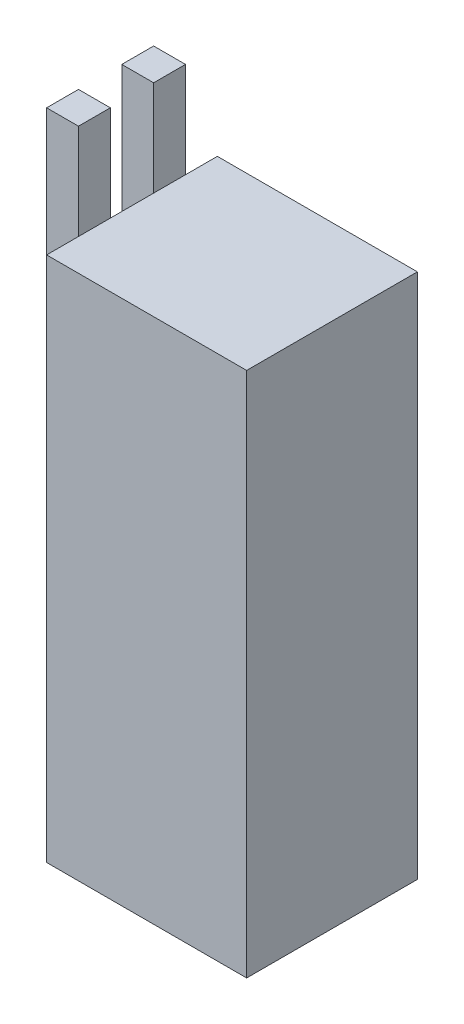
SolidWorks part; units mm, degrees
ref_plane "Front" through (0, 0, 0) normal (0, 0, 1) x (1, 0, 0)
ref_plane "Top" through (0, 0, 0) normal (0, 1, 0) x (1, 0, 0)
ref_plane "Right" through (0, 0, 0) normal (1, 0, 0) x (0, 0, -1)
sketch "Sketch1" plane through (0, 0, 0) normal (0, 1, 0) x (1, 0, 0)
  line L1 (-19.939, -17.018) -> (19.939, -17.018)
  line L2 (-19.939, -17.018) -> (-19.939, 17.018)
  line L3 (-19.939, 17.018) -> (19.939, 17.018)
  line L4 (19.939, -17.018) -> (19.939, 17.018)
  line L5 (-19.939, -17.018) -> (19.939, 17.018) construction
  line L6 (-19.939, 17.018) -> (19.939, -17.018) construction
  point P0 (0, 0)
  dimension "D1" = 34.036
  dimension "D2" = 39.878
extrude "Boss-Extrude1" add sketch "Sketch1" along normal blind 104.902
sketch "Sketch3" plane through (-19.939, 0, -2.921) normal (1, 0, 0) x (0, 0, -1)
  line L1 (1.397, 98.552) -> (7.747, 98.552)
  line L2 (1.397, 98.552) -> (1.397, 123.952)
  line L3 (1.397, 123.952) -> (7.747, 123.952)
  line L4 (7.747, 98.552) -> (7.747, 123.952)
  line L5 (-7.239, 98.552) -> (-13.589, 98.552)
  line L6 (-7.239, 98.552) -> (-7.239, 123.952)
  line L7 (-7.239, 123.952) -> (-13.589, 123.952)
  line L8 (-13.589, 98.552) -> (-13.589, 123.952)
  line L11 (14.097, 104.902) -> (-19.939, 104.902) construction
  line L12 (14.097, 104.902) -> (14.097, 0) construction
  line L13 (-19.939, 104.902) -> (-19.939, 0) construction
  dimension "D1" = 6.35
  dimension "D2" = 6.35
  dimension "D3" = 6.35
  dimension "D4" = 25.4
  dimension "D5" = 6.35
extrude "Boss-Extrude2" add sketch "Sketch3" against normal blind 6.35
